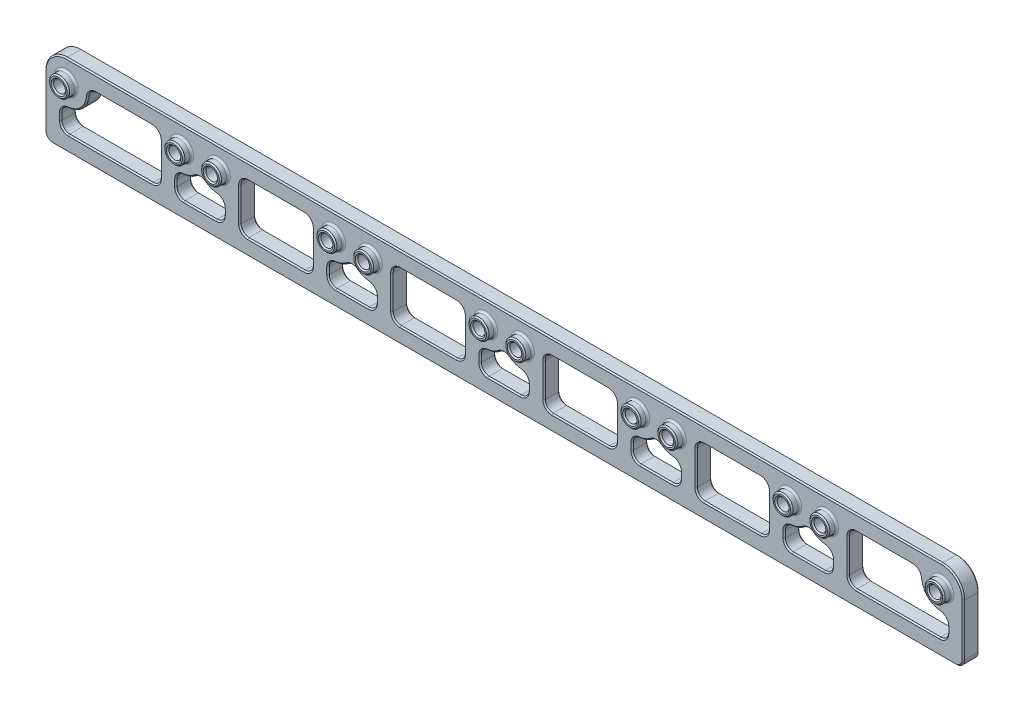
SolidWorks part; units mm, degrees
ref_plane "Front Plane" through (0, 0, 0) normal (0, 0, 1) x (1, 0, 0)
ref_plane "Top Plane" through (0, 0, 0) normal (0, 1, 0) x (1, 0, 0)
ref_plane "Right Plane" through (0, 0, 0) normal (1, 0, 0) x (0, 0, -1)
sketch "Sketch1" plane through (0, 0, 0) normal (0, 0, 1) x (1, 0, 0)
  line L0 (-92.075, 0) -> (92.075, 0) construction
  line L1 (-92.075, 4.3205) -> (92.075, 4.3205)
  line L2 (92.075, 4.3205) -> (92.075, -11.999)
  line L3 (92.075, -11.999) -> (-92.075, -11.999)
  line L4 (-92.075, -11.999) -> (-92.075, 4.3205)
  dimension "D1" = 184.15
  dimension "D2" = 11.999
  dimension "D3" = 4.3205
extrude "Boss-Extrude1" add sketch "Sketch1" along normal mid plane 3.175
sketch "Sketch2" plane through (0, 0, 1.5875) normal (0, 0, 1) x (1, 0, 0)
  line L0 (-3.6855, 0) -> (3.6855, 0) construction
  line L1 (-87.7545, 0) -> (-64.6455, 0) construction
  line L2 (-64.6455, 0) -> (-57.2745, 0) construction
  line L3 (-57.2745, 0) -> (-34.1655, 0) construction
  line L4 (-34.1655, 0) -> (-26.7945, 0) construction
  line L5 (-26.7945, 0) -> (-3.6855, 0) construction
  line L6 (3.6855, 0) -> (26.7945, 0) construction
  line L7 (26.7945, 0) -> (34.1655, 0) construction
  line L8 (34.1655, 0) -> (57.2745, 0) construction
  line L9 (57.2745, 0) -> (64.6455, 0) construction
  line L10 (64.6455, 0) -> (87.7545, 0) construction
  circle A0 centre (-87.7545, 0) radius 2.0002
  circle A1 centre (-64.6455, 0) radius 2.0002
  circle A2 centre (-57.2745, 0) radius 2.0003
  circle A3 centre (-34.1655, 0) radius 2.0003
  circle A4 centre (-26.7945, 0) radius 2.0003
  circle A5 centre (-3.6855, 0) radius 2.0002
  circle A6 centre (3.6855, 0) radius 2.0003
  circle A7 centre (26.7945, 0) radius 2.0002
  circle A8 centre (34.1655, 0) radius 2.0003
  circle A9 centre (57.2745, 0) radius 2.0003
  circle A10 centre (64.6455, 0) radius 2.0002
  circle A11 centre (87.7545, 0) radius 2.0002
  dimension "D1" = 4.0005
  dimension "D2" = 23.1089
  dimension "D3" = 7.3711
  dimension "D4" = 23.1089
  dimension "D5" = 7.3711
  dimension "D6" = 23.1089
  dimension "D7" = 7.3711
  dimension "D8" = 23.1089
  dimension "D9" = 7.3711
  dimension "D10" = 23.1089
  dimension "D11" = 7.3711
  dimension "D12" = 23.1089
extrude "Boss-Extrude2" add sketch "Sketch2" along normal blind 1.5875 contours A0
hole_wizard "3/32 (0.09375) Diameter Hole1" positions "Sketch3" profile "Sketch4" hole size "3/32" standard "ANSI Inch" end condition through all
sketch "Sketch3" plane through (0, 0, 3.175) normal (0, 0, 1) x (1, 0, 0)
  circle A0 centre (-87.7545, 0) radius 2.0002 construction
  point P0 (-87.7545, 0)
  point P2 (-64.6455, 0)
  point P5 (-57.2745, 0)
  point P8 (-34.1655, 0)
  point P11 (-26.7945, 0)
  point P14 (-3.6855, 0)
  point P17 (3.6855, 0)
  point P20 (26.7945, 0)
  point P23 (34.1655, 0)
  point P26 (57.2745, 0)
  point P29 (64.6455, 0)
  point P32 (87.7545, 0)
sketch "Sketch4" plane through (-87.7545, 0, 3.175) normal (1, 0, 0) x (0, -1, 0)
  line L0 (0, 0) -> (0, 4.7625)
  line L1 (0, 4.7625) -> (1.1906, 4.7625)
  line L2 (1.1906, 4.7625) -> (1.1906, 0)
  line L5 (1.1906, 0) -> (0, 0)
  line L11 (0, -6.35) -> (0, 107.95) construction
  dimension "Thru Hole Dia." = 2.3812
  dimension "Thru Hole Depth" = 4.7625
sketch "Sketch5" plane through (0, 0, 0) normal (0, 0, 1) x (1, 0, 0)
  line L0 (92.075, 4.3205) -> (-92.075, 4.3205) construction
  line L1 (-83.5844, 1.1303) -> (-68.8156, 1.1303)
  line L2 (-53.1044, 1.1303) -> (-38.3356, 1.1303)
  line L3 (-22.6244, 1.1303) -> (-7.8556, 1.1303)
  line L4 (7.8556, 1.1303) -> (22.6244, 1.1303)
  line L5 (38.3356, 1.1303) -> (53.1044, 1.1303)
  line L6 (68.8156, 1.1303) -> (83.5844, 1.1303)
  line L7 (-88.8848, -4.1701) -> (-88.8848, -8.8087)
  line L8 (-88.8848, -8.8087) -> (-68.9661, -8.8087)
  line L9 (-68.9661, -8.8087) -> (-68.9661, 0)
  line L10 (-65.7758, -4.1701) -> (-65.7758, -8.8087)
  line L11 (-65.7758, -8.8087) -> (-56.1442, -8.8087)
  line L12 (-56.1442, -8.8087) -> (-56.1442, -4.1701)
  line L13 (-52.9539, 0) -> (-52.9539, -8.8087)
  line L14 (-52.9539, -8.8087) -> (-38.4861, -8.8087)
  line L15 (-38.4861, -8.8087) -> (-38.4861, 0)
  line L16 (-35.2958, -4.1701) -> (-35.2958, -8.8087)
  line L17 (-35.2958, -8.8087) -> (-25.6642, -8.8087)
  line L18 (-25.6642, -8.8087) -> (-25.6642, -4.1701)
  line L19 (-22.4739, 0) -> (-22.4739, -8.8087)
  line L20 (-22.4739, -8.8087) -> (-8.0061, -8.8087)
  line L21 (-8.0061, -8.8087) -> (-8.0061, 0)
  line L22 (-4.8158, -4.1701) -> (-4.8158, -8.8087)
  line L23 (-4.8158, -8.8087) -> (4.8158, -8.8087)
  line L24 (4.8158, -8.8087) -> (4.8158, -4.1701)
  line L25 (8.0061, 0) -> (8.0061, -8.8087)
  line L26 (8.0061, -8.8087) -> (22.4739, -8.8087)
  line L27 (22.4739, -8.8087) -> (22.4739, 0)
  line L28 (25.6642, -4.1701) -> (25.6642, -8.8087)
  line L29 (25.6642, -8.8087) -> (35.2958, -8.8087)
  line L30 (35.2958, -8.8087) -> (35.2958, -4.1701)
  line L31 (38.4861, 0) -> (38.4861, -8.8087)
  line L32 (38.4861, -8.8087) -> (52.9539, -8.8087)
  line L33 (52.9539, -8.8087) -> (52.9539, 0)
  line L34 (56.1442, -4.1701) -> (56.1442, -8.8087)
  line L35 (56.1442, -8.8087) -> (65.7758, -8.8087)
  line L36 (65.7758, -8.8087) -> (65.7758, -4.1701)
  line L37 (68.9661, 0) -> (68.9661, -8.8087)
  line L38 (68.9661, -8.8087) -> (88.8848, -8.8087)
  line L39 (88.8848, -8.8087) -> (88.8848, -4.1701)
  line L40 (-92.075, 0) -> (-92.075, 4.3205)
  line L41 (-92.075, 4.3205) -> (-87.7545, 4.3205)
  line L42 (87.7545, 4.3205) -> (92.075, 4.3205)
  line L43 (92.075, 4.3205) -> (92.075, 0)
  line L44 (-88.8848, -6.4894) -> (-92.075, -6.4894) construction
  line L45 (-92.075, 4.3205) -> (-92.075, -11.999) construction
  line L46 (-92.075, -11.999) -> (92.075, -11.999) construction
  line L48 (-76.2, 1.1303) -> (-76.2, 4.3205) construction
  line L49 (-65.7758, -6.4894) -> (-68.9661, -6.4894) construction
  line L50 (-56.1442, -6.4894) -> (-52.9539, -6.4894) construction
  line L51 (-35.2958, -6.4894) -> (-38.4861, -6.4894) construction
  line L52 (-25.6642, -6.4894) -> (-22.4739, -6.4894) construction
  line L53 (-4.8158, -6.4894) -> (-8.0061, -6.4894) construction
  line L54 (4.8158, -6.4894) -> (8.0061, -6.4894) construction
  line L55 (25.6642, -6.4894) -> (22.4739, -6.4894) construction
  line L56 (35.2958, -6.4894) -> (38.4861, -6.4894) construction
  line L57 (56.1442, -6.4894) -> (52.9539, -6.4894) construction
  line L58 (65.7758, -6.4894) -> (68.9661, -6.4894) construction
  line L59 (88.8848, -6.4894) -> (92.075, -6.4894) construction
  line L60 (92.075, -11.999) -> (92.075, 4.3205) construction
  arc A0 (-87.7545, 4.3205) -> (-92.075, 0) centre (-87.7545, 0) ccw
  arc A1 (-68.8156, 1.1303) -> (-68.9661, 0) centre (-64.6455, 0) ccw
  arc A2 (-60.96, -2.2547) -> (-56.1442, -4.1701) centre (-57.2745, 0) ccw
  arc A3 (-38.3356, 1.1303) -> (-38.4861, 0) centre (-34.1655, 0) ccw
  arc A4 (-30.48, -2.2547) -> (-25.6642, -4.1701) centre (-26.7945, 0) ccw
  arc A5 (-7.8556, 1.1303) -> (-8.0061, 0) centre (-3.6855, 0) ccw
  arc A6 (0, -2.2547) -> (4.8158, -4.1701) centre (3.6855, 0) ccw
  arc A7 (22.6244, 1.1303) -> (22.4739, 0) centre (26.7945, 0) ccw
  arc A8 (30.48, -2.2547) -> (35.2958, -4.1701) centre (34.1655, 0) ccw
  arc A9 (53.1044, 1.1303) -> (52.9539, 0) centre (57.2745, 0) ccw
  arc A10 (60.96, -2.2547) -> (65.7758, -4.1701) centre (64.6455, 0) ccw
  arc A11 (83.5844, 1.1303) -> (88.8848, -4.1701) centre (87.7545, 0) ccw
  arc A12 (-88.8848, -4.1701) -> (-83.5844, 1.1303) centre (-87.7545, 0) ccw
  arc A13 (-65.7758, -4.1701) -> (-60.96, -2.2547) centre (-64.6455, 0) ccw
  arc A14 (-52.9539, 0) -> (-53.1044, 1.1303) centre (-57.2745, 0) ccw
  arc A15 (-35.2958, -4.1701) -> (-30.48, -2.2547) centre (-34.1655, 0) ccw
  arc A16 (-22.4739, 0) -> (-22.6244, 1.1303) centre (-26.7945, 0) ccw
  arc A17 (-4.8158, -4.1701) -> (0, -2.2547) centre (-3.6855, 0) ccw
  arc A18 (8.0061, 0) -> (7.8556, 1.1303) centre (3.6855, 0) ccw
  arc A19 (25.6642, -4.1701) -> (30.48, -2.2547) centre (26.7945, 0) ccw
  arc A20 (38.4861, 0) -> (38.3356, 1.1303) centre (34.1655, 0) ccw
  arc A21 (56.1442, -4.1701) -> (60.96, -2.2547) centre (57.2745, 0) ccw
  arc A22 (68.9661, 0) -> (68.8156, 1.1303) centre (64.6455, 0) ccw
  arc A23 (92.075, 0) -> (87.7545, 4.3205) centre (87.7545, 0) ccw
  dimension "D1" = 3.1902
  dimension "D2" = 3.1902
  dimension "D3" = 3.1902
extrude "Cut-Extrude1" cut sketch "Sketch5" against normal through all both and the other way through all contours L1 A1 L9 L8 L7 A12
fillet "Fillet1" radius 0.3969 12 edges at (85.7542, 0, 1.5875) (62.6453, 0, 1.5875) (55.2742, 0, 1.5875) (32.1653, 0, 1.5875) (24.7942, 0, 1.5875) (1.6853, 0, 1.5875) (-5.6858, 0, 1.5875) (-28.7947, 0, 1.5875) (-36.1658, 0, 1.5875) (-59.2747, 0, 1.5875) (-66.6458, 0, 1.5875) (-89.7547, 0, 1.5875)
fillet "Fillet2" radius 1.5875 53 edges at (-92.075, -11.999, 0) (92.075, -11.999, 0) (88.8848, -8.8087, 0) (88.8848, -4.1701, 0) (83.5844, 1.1303, 0) (68.8156, 1.1303, 0) (68.9661, -8.8087, 0) (65.7758, -8.8087, 0) (56.1442, -8.8087, 0) (56.1442, -4.1701, 0) (60.96, -2.2547, 0) (53.1044, 1.1303, 0) (38.3356, 1.1303, 0) (38.4861, -8.8087, 0) (52.9539, -8.8087, 0) (35.2958, -8.8087, 0) (35.2958, -4.1701, 0) (30.48, -2.2547, 0) (25.6642, -4.1701, 0) (25.6642, -8.8087, 0) (22.4739, -8.8087, 0) (22.6244, 1.1303, 0) (7.8556, 1.1303, 0) (8.0061, -8.8087, 0) (4.8158, -8.8087, 0) (4.8158, -4.1701, 0) (0, -2.2547, 0) (-4.8158, -4.1701, 0) (-4.8158, -8.8087, 0) (-8.0061, -8.8087, 0) (-22.4739, -8.8087, 0) (-22.6244, 1.1303, 0) (-7.8556, 1.1303, 0) (-25.6642, -8.8087, 0) (-25.6642, -4.1701, 0) (-30.48, -2.2547, 0) (-35.2958, -4.1701, 0) (-35.2958, -8.8087, 0) (-38.3356, 1.1303, 0) (-38.4861, -8.8087, 0) (-52.9539, -8.8087, 0) (-53.1044, 1.1303, 0) (-56.1442, -8.8087, 0) (-56.1442, -4.1701, 0) (-60.96, -2.2547, 0) (-65.7758, -4.1701, 0) (-65.7758, -8.8087, 0) (-68.9661, -8.8087, 0) (-68.8156, 1.1303, 0) (-88.8848, -8.8087, 0) (-88.8848, -4.1701, 0) (-83.5844, 1.1303, 0) (65.7758, -4.1701, 0)
chamfer "Chamfer2" distance 0.254 angle 45 256 edges at (89.7547, 0, 3.175) (66.6458, 0, 3.175) (59.2747, 0, 3.175) (36.1658, 0, 3.175) (28.7947, 0, 3.175) (5.6858, 0, 3.175) (-1.6853, 0, 3.175) (-24.7942, 0, 3.175) (-32.1653, 0, 3.175) (-55.2742, 0, 3.175) (-62.6453, 0, 3.175) (-85.7542, 0, 3.175) (88.9451, 0, 3.175) (88.9451, 0, -1.5875) (65.8362, 0, 3.175) (65.8362, 0, -1.5875) (58.4651, 0, 3.175) (58.4651, 0, -1.5875) (35.3562, 0, 3.175) (35.3562, 0, -1.5875) (27.9851, 0, 3.175) (27.9851, 0, -1.5875) (4.8762, 0, 3.175) (4.8762, 0, -1.5875) (-2.4949, 0, 3.175) (-2.4949, 0, -1.5875) (-25.6038, 0, 3.175) (-25.6038, 0, -1.5875) (-32.9749, 0, 3.175) (-32.9749, 0, -1.5875) (-56.0838, 0, 3.175) (-56.0838, 0, -1.5875) (-63.4549, 0, 3.175) (-63.4549, 0, -1.5875) (-86.5638, 0, 3.175) (-86.5638, 0, -1.5875) (-56.5665, -4.8121, -1.5875) (-56.1442, -6.5558, -1.5875) (-56.6091, -8.3438, -1.5875) (-60.96, -8.8087, -1.5875) (-65.3109, -8.3438, -1.5875) (-65.7758, -6.5558, -1.5875) (-65.3535, -4.8121, -1.5875) (-63.0609, -4.0194, -1.5875) (-60.96, -3.03, -1.5875) (-58.8591, -4.0194, -1.5875) (52.489, 0.6653, -1.5875) (52.9539, -3.8392, -1.5875) (52.489, -8.3438, -1.5875) (45.72, -8.8087, -1.5875) (38.951, -8.3438, -1.5875) (38.4861, -3.8392, -1.5875) (38.951, 0.6653, -1.5875) (45.72, 1.1303, -1.5875) (82.9424, 0.708, -1.5875) (84.6994, -3.0551, -1.5875) (88.4624, -4.8121, -1.5875) (88.8848, -6.5558, -1.5875) (88.4198, -8.3438, -1.5875) (78.9254, -8.8087, -1.5875) (69.431, -8.3438, -1.5875) (68.9661, -3.8392, -1.5875) (69.431, 0.6653, -1.5875) (76.2089, 1.1303, -1.5875) (91.61, -11.534, -1.5875) (92.075, -5.2057, -1.5875) (90.8095, 3.0551, -1.5875) (0, 4.3205, -1.5875) (-90.8095, 3.0551, -1.5875) (-92.075, -5.2057, -1.5875) (-91.61, -11.534, -1.5875) (0, -11.999, -1.5875) (-26.0865, -4.8121, -1.5875) (-25.6642, -6.5558, -1.5875) (-26.1291, -8.3438, -1.5875) (-30.48, -8.8087, -1.5875) (-34.8309, -8.3438, -1.5875) (-35.2958, -6.5558, -1.5875) (-34.8735, -4.8121, -1.5875) (-32.5809, -4.0194, -1.5875) (-30.48, -3.03, -1.5875) (-28.3791, -4.0194, -1.5875) (4.3935, -4.8121, -1.5875) (4.8158, -6.5558, -1.5875) (4.3509, -8.3438, -1.5875) (0, -8.8087, -1.5875) (-4.3509, -8.3438, -1.5875) (-4.8158, -6.5558, -1.5875) (-4.3935, -4.8121, -1.5875) (-2.1009, -4.0194, -1.5875) (0, -3.03, -1.5875) (2.1009, -4.0194, -1.5875) (34.8735, -4.8121, -1.5875) (35.2958, -6.5558, -1.5875) (34.8309, -8.3438, -1.5875) (30.48, -8.8087, -1.5875) (26.1291, -8.3438, -1.5875) (25.6642, -6.5558, -1.5875) (26.0865, -4.8121, -1.5875) (28.3791, -4.0194, -1.5875) (30.48, -3.03, -1.5875) (32.5809, -4.0194, -1.5875) (65.7758, -6.5558, -1.5875) (65.3109, -8.3438, -1.5875) (60.96, -8.8087, -1.5875) (56.6091, -8.3438, -1.5875) (56.1442, -6.5558, -1.5875) (56.5665, -4.8121, -1.5875) (58.8591, -4.0194, -1.5875) (60.96, -3.03, -1.5875) (63.0609, -4.0194, -1.5875) (-69.431, 0.6653, -1.5875) (-68.9661, -3.8392, -1.5875) (-69.431, -8.3438, -1.5875) (-78.9254, -8.8087, -1.5875) (-88.4198, -8.3438, -1.5875) (-88.8848, -6.5558, -1.5875) (-88.4624, -4.8121, -1.5875) (-84.6994, -3.0551, -1.5875) (-82.9424, 0.708, -1.5875) (-76.2089, 1.1303, -1.5875) (-38.951, 0.6653, -1.5875) (-38.4861, -3.8392, -1.5875) (-38.951, -8.3438, -1.5875) (-45.72, -8.8087, -1.5875) (-52.489, -8.3438, -1.5875) (-52.9539, -3.8392, -1.5875) (-52.489, 0.6653, -1.5875) (-45.72, 1.1303, -1.5875) (-8.471, 0.6653, -1.5875) (-8.0061, -3.8392, -1.5875) (-8.471, -8.3438, -1.5875) (-15.24, -8.8087, -1.5875) (-22.009, -8.3438, -1.5875) (-22.4739, -3.8392, -1.5875) (-22.009, 0.6653, -1.5875) (-15.24, 1.1303, -1.5875) (22.009, 0.6653, -1.5875) (22.4739, -3.8392, -1.5875) (22.009, -8.3438, -1.5875) (15.24, -8.8087, -1.5875) (8.471, -8.3438, -1.5875) (8.0061, -3.8392, -1.5875) (8.471, 0.6653, -1.5875) (15.24, 1.1303, -1.5875) (-90.8095, 3.0551, 1.5875) (0, 4.3205, 1.5875) (90.8095, 3.0551, 1.5875) (92.075, -5.2057, 1.5875) (91.61, -11.534, 1.5875) (0, -11.999, 1.5875) (-91.61, -11.534, 1.5875) (-92.075, -5.2057, 1.5875) (-56.6091, -8.3438, 1.5875) (-56.1442, -6.5558, 1.5875) (-56.5665, -4.8121, 1.5875) (-58.8591, -4.0194, 1.5875) (-60.96, -3.03, 1.5875) (-63.0609, -4.0194, 1.5875) (-65.3535, -4.8121, 1.5875) (-65.7758, -6.5558, 1.5875) (-65.3109, -8.3438, 1.5875) (-60.96, -8.8087, 1.5875) (52.489, -8.3438, 1.5875) (52.9539, -3.8392, 1.5875) (52.489, 0.6653, 1.5875) (45.72, 1.1303, 1.5875) (38.951, 0.6653, 1.5875) (38.4861, -3.8392, 1.5875) (38.951, -8.3438, 1.5875) (45.72, -8.8087, 1.5875) (88.4198, -8.3438, 1.5875) (88.8848, -6.5558, 1.5875) (88.4624, -4.8121, 1.5875) (84.6994, -3.0551, 1.5875) (82.9424, 0.708, 1.5875) (76.2089, 1.1303, 1.5875) (69.431, 0.6653, 1.5875) (68.9661, -3.8392, 1.5875) (69.431, -8.3438, 1.5875) (78.9254, -8.8087, 1.5875) (-26.1291, -8.3438, 1.5875) (-25.6642, -6.5558, 1.5875) (-26.0865, -4.8121, 1.5875) (-28.3791, -4.0194, 1.5875) (-30.48, -3.03, 1.5875) (-32.5809, -4.0194, 1.5875) (-34.8735, -4.8121, 1.5875) (-35.2958, -6.5558, 1.5875) (-34.8309, -8.3438, 1.5875) (-30.48, -8.8087, 1.5875) (4.3509, -8.3438, 1.5875) (4.8158, -6.5558, 1.5875) (4.3935, -4.8121, 1.5875) (2.1009, -4.0194, 1.5875) (0, -3.03, 1.5875) (-2.1009, -4.0194, 1.5875) (-4.3935, -4.8121, 1.5875) (-4.8158, -6.5558, 1.5875) (-4.3509, -8.3438, 1.5875) (0, -8.8087, 1.5875) (34.8309, -8.3438, 1.5875) (35.2958, -6.5558, 1.5875) (34.8735, -4.8121, 1.5875) (32.5809, -4.0194, 1.5875) (30.48, -3.03, 1.5875) (28.3791, -4.0194, 1.5875) (26.0865, -4.8121, 1.5875) (25.6642, -6.5558, 1.5875) (26.1291, -8.3438, 1.5875) (30.48, -8.8087, 1.5875) (65.3109, -8.3438, 1.5875) (65.7758, -6.5558, 1.5875) (63.0609, -4.0194, 1.5875) (60.96, -3.03, 1.5875) (58.8591, -4.0194, 1.5875) (56.5665, -4.8121, 1.5875) (56.1442, -6.5558, 1.5875) (56.6091, -8.3438, 1.5875) (60.96, -8.8087, 1.5875) (-69.431, -8.3438, 1.5875) (-68.9661, -3.8392, 1.5875) (-69.431, 0.6653, 1.5875) (-76.2089, 1.1303, 1.5875) (-82.9424, 0.708, 1.5875) (-84.6994, -3.0551, 1.5875) (-88.4624, -4.8121, 1.5875) (-88.8848, -6.5558, 1.5875) (-88.4198, -8.3438, 1.5875) (-78.9254, -8.8087, 1.5875) (-38.951, -8.3438, 1.5875) (-38.4861, -3.8392, 1.5875) (-38.951, 0.6653, 1.5875) (-45.72, 1.1303, 1.5875) (-52.489, 0.6653, 1.5875) (-52.9539, -3.8392, 1.5875) (-52.489, -8.3438, 1.5875) (-45.72, -8.8087, 1.5875) (-8.471, -8.3438, 1.5875) (-8.0061, -3.8392, 1.5875) (-8.471, 0.6653, 1.5875) (-15.24, 1.1303, 1.5875) (-22.009, 0.6653, 1.5875) (-22.4739, -3.8392, 1.5875) (-22.009, -8.3438, 1.5875) (-15.24, -8.8087, 1.5875) (22.009, -8.3438, 1.5875) (22.4739, -3.8392, 1.5875) (22.009, 0.6653, 1.5875) (15.24, 1.1303, 1.5875) (8.471, 0.6653, 1.5875) (8.0061, -3.8392, 1.5875) (8.471, -8.3438, 1.5875) (15.24, -8.8087, 1.5875) (65.3535, -4.8121, -1.5875) (65.3535, -4.8121, 1.5875)
equation "\"D3@Sketch5\"=\"D2@Sketch5\""
